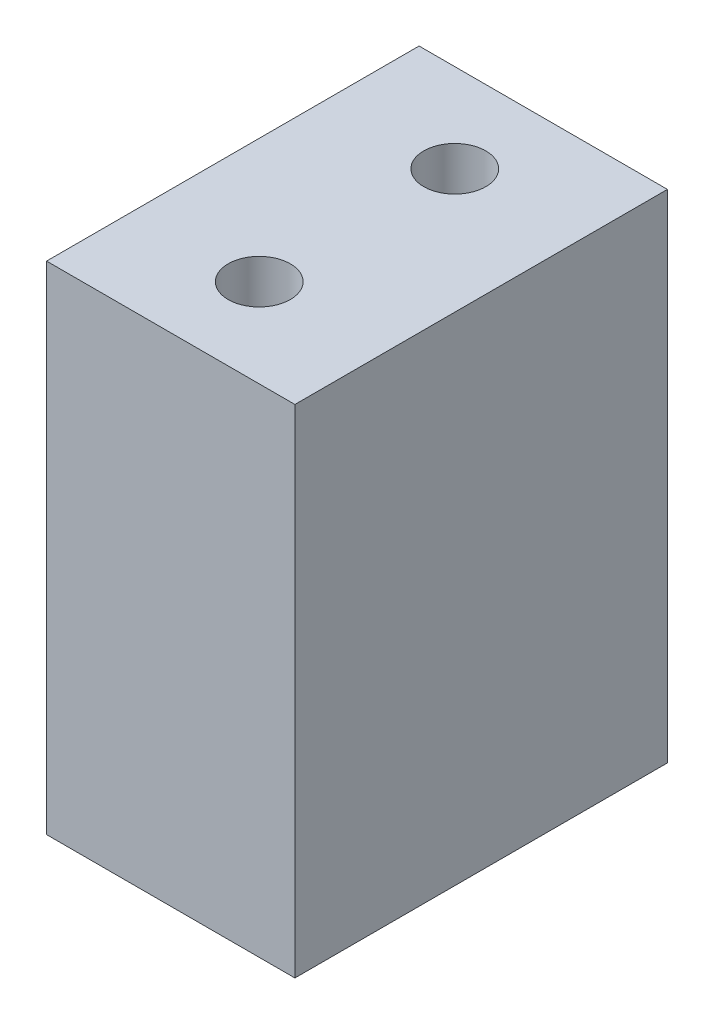
SolidWorks part; units mm, degrees
material "Delrin 2700 NC010, Low Viscosity Acetal Copolymer (SS)"
ref_plane "Front Plane" through (0, 0, 0) normal (0, 0, 1) x (1, 0, 0)
ref_plane "Top Plane" through (0, 0, 0) normal (0, 1, 0) x (1, 0, 0)
ref_plane "Right Plane" through (0, 0, 0) normal (1, 0, 0) x (0, 0, -1)
sketch "Sketch1" plane through (0, 0, 0) normal (0, 1, 0) x (1, 0, 0)
  line L0 (0, 10) -> (0, -10) construction
  line L1 (-12.7, -19.05) -> (12.7, -19.05)
  line L2 (-12.7, -19.05) -> (-12.7, 19.05)
  line L3 (-12.7, 19.05) -> (12.7, 19.05)
  line L4 (12.7, -19.05) -> (12.7, 19.05)
  line L5 (-12.7, -19.05) -> (12.7, 19.05) construction
  line L6 (-12.7, 19.05) -> (12.7, -19.05) construction
  circle A0 centre (0, 10) radius 3.175
  circle A1 centre (0, -10) radius 3.175
  point P0 (0, 0)
  point P8 (0, 0)
  dimension "D3" = 20
  dimension "D4" = 6.35
  dimension "D1" = 38.1
  dimension "D2" = 25.4
extrude "Boss-Extrude1" add sketch "Sketch1" along normal blind 50.8
